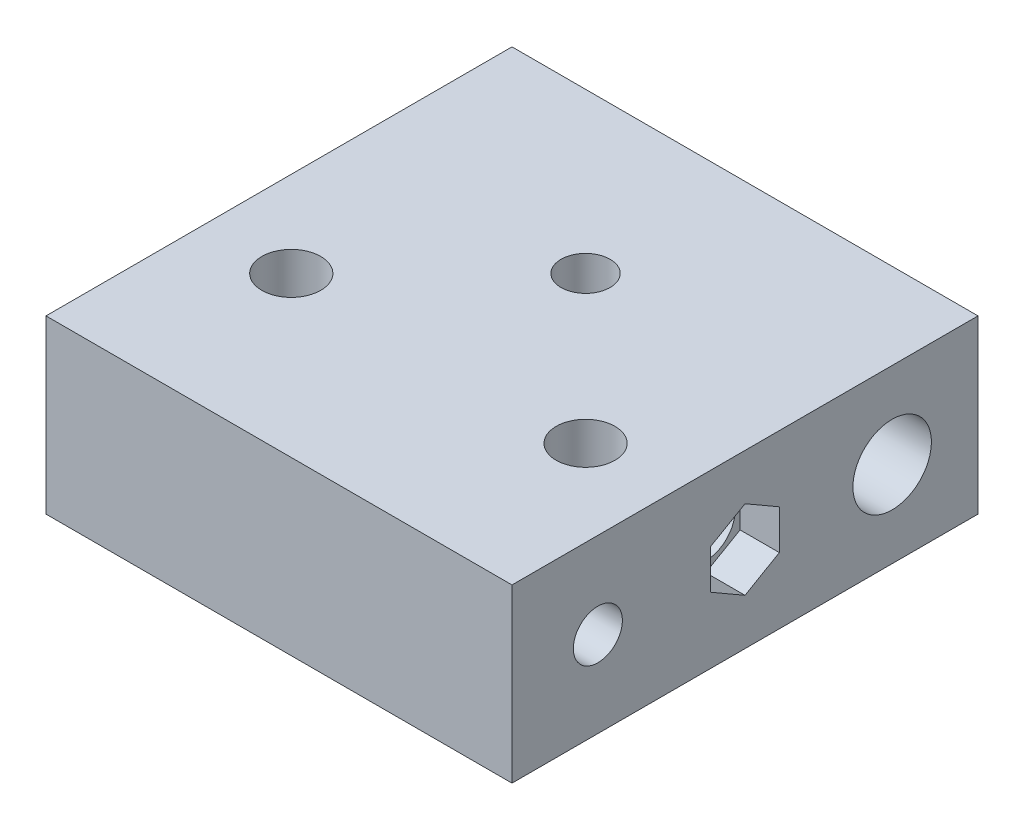
SolidWorks part; units mm, degrees
ref_plane "Front Plane" through (0, 0, 0) normal (0, 0, 1) x (1, 0, 0)
ref_plane "Top Plane" through (0, 0, 0) normal (0, 1, 0) x (1, 0, 0)
ref_plane "Right Plane" through (0, 0, 0) normal (1, 0, 0) x (0, 0, -1)
sketch "Sketch1" plane through (0, 0, 0) normal (0, 0, 1) x (1, 0, 0)
  line L1 (-47.5, 17.5) -> (47.5, 17.5)
  line L2 (-47.5, 17.5) -> (-47.5, -17.5)
  line L3 (-47.5, -17.5) -> (47.5, -17.5)
  line L4 (47.5, 17.5) -> (47.5, -17.5)
  line L5 (-47.5, 17.5) -> (47.5, -17.5) construction
  line L6 (-47.5, -17.5) -> (47.5, 17.5) construction
  point P0 (0, 0)
  dimension "D1" = 35
  dimension "D2" = 95
extrude "Boss-Extrude1" add sketch "Sketch1" along normal blind 95
sketch "Sketch2" plane through (-47.5, 0, 0) normal (-1, 0, 0) x (0, 0, 1)
  line L1 (95, 17.5) -> (95, -17.5) construction
  line L2 (0, 17.5) -> (0, -17.5) construction
  line L3 (95, -17.5) -> (0, -17.5) construction
  circle A0 centre (17.5, 0) radius 5
  circle A1 centre (47.5, 0) radius 6
  circle A2 centre (77.5, 0) radius 5
  dimension "D1" = 12
  dimension "D2" = 10
  dimension "D3" = 10
  dimension "D4" = 47.5
  dimension "D5" = 17.5
  dimension "D6" = 17.5
  dimension "D7" = 17.5
  dimension "D8" = 17.5
  dimension "D9" = 17.5
extrude "Cut-Extrude1" cut sketch "Sketch2" against normal blind 95
sketch "Sketch3" plane through (-47.5, 0, 0) normal (-1, 0, 0) x (0, 0, 1)
  circle A0 centre (17.5, 0) radius 8
  dimension "D1" = 16
extrude "Cut-Extrude2" cut sketch "Sketch3" against normal blind 26
sketch "Sketch4" plane through (-47.5, 0, 0) normal (-1, 0, 0) x (0, 0, 1)
  circle A0 centre (77.5, 0) radius 8
  dimension "D1" = 16
extrude "Cut-Extrude3" cut sketch "Sketch4" against normal blind 60
sketch "Sketch5" plane through (47.5, 0, 0) normal (1, 0, 0) x (0, 0, -1)
  circle A0 centre (-17.5, 0) radius 8
  dimension "D1" = 16
extrude "Cut-Extrude4" cut sketch "Sketch5" against normal blind 26
sketch "Sketch6" plane through (0, 17.5, 0) normal (0, 1, 0) x (1, 0, 0)
  line L0 (47.5, -95) -> (-47.5, -95) construction
  line L1 (47.5, 0) -> (-47.5, 0) construction
  line L2 (-47.5, -95) -> (-47.5, 0) construction
  line L3 (47.5, -95) -> (47.5, 0) construction
  circle A0 centre (0, -32.5) radius 5
  circle A1 centre (-30, -62.5) radius 6
  circle A2 centre (30, -62.5) radius 6
  dimension "D1" = 10
  dimension "D2" = 12
  dimension "D3" = 12
  dimension "D4" = 32.5
  dimension "D5" = 32.5
  dimension "D6" = 32.5
  dimension "D7" = 17.5
  dimension "D8" = 17.5
  dimension "D9" = 47.5
extrude "Cut-Extrude5" cut sketch "Sketch6" against normal blind 35 from surface at 0 starting at face at (0, 17.5, 47.5)
sketch "Sketch8" plane through (0, -17.5, 0) normal (0, -1, 0) x (1, 0, 0)
  circle A1 centre (30, 62.5) radius 8
  dimension "D1" = 16
extrude "Cut-Extrude7" cut sketch "Sketch8" against normal blind 26
sketch "Sketch12" plane through (0, -17.5, 0) normal (0, -1, 0) x (1, 0, 0)
  line L1 (8.0829, 32.5) -> (4.0415, 39.5)
  line L2 (4.0415, 39.5) -> (-4.0415, 39.5)
  line L3 (-4.0415, 39.5) -> (-8.0829, 32.5)
  line L4 (-8.0829, 32.5) -> (-4.0415, 25.5)
  line L5 (-4.0415, 25.5) -> (4.0415, 25.5)
  line L6 (4.0415, 25.5) -> (8.0829, 32.5)
  circle A0 centre (0, 32.5) radius 7 construction
  dimension "14" = 14
extrude "Cut-Extrude10" cut sketch "Sketch12" against normal blind 8
sketch "Sketch16" plane through (-47.5, 0, 0) normal (-1, 0, 0) x (0, 0, 1)
  line L1 (47.5, -8.0829) -> (54.5, -4.0415)
  line L2 (54.5, -4.0415) -> (54.5, 4.0415)
  line L3 (54.5, 4.0415) -> (47.5, 8.0829)
  line L4 (47.5, 8.0829) -> (40.5, 4.0415)
  line L5 (40.5, 4.0415) -> (40.5, -4.0415)
  line L6 (40.5, -4.0415) -> (47.5, -8.0829)
  circle A0 centre (47.5, 0) radius 7 construction
  dimension "D1" = 14
extrude "Cut-Extrude14" cut sketch "Sketch16" against normal blind 8
sketch "Sketch17" plane through (47.5, 0, 0) normal (1, 0, 0) x (0, 0, -1)
  line L1 (-47.5, -8.0829) -> (-40.5, -4.0415)
  line L2 (-40.5, -4.0415) -> (-40.5, 4.0415)
  line L3 (-40.5, 4.0415) -> (-47.5, 8.0829)
  line L4 (-47.5, 8.0829) -> (-54.5, 4.0415)
  line L5 (-54.5, 4.0415) -> (-54.5, -4.0415)
  line L6 (-54.5, -4.0415) -> (-47.5, -8.0829)
  circle A0 centre (-47.5, 0) radius 7 construction
  dimension "D1" = 14
extrude "Cut-Extrude15" cut sketch "Sketch17" against normal blind 8
